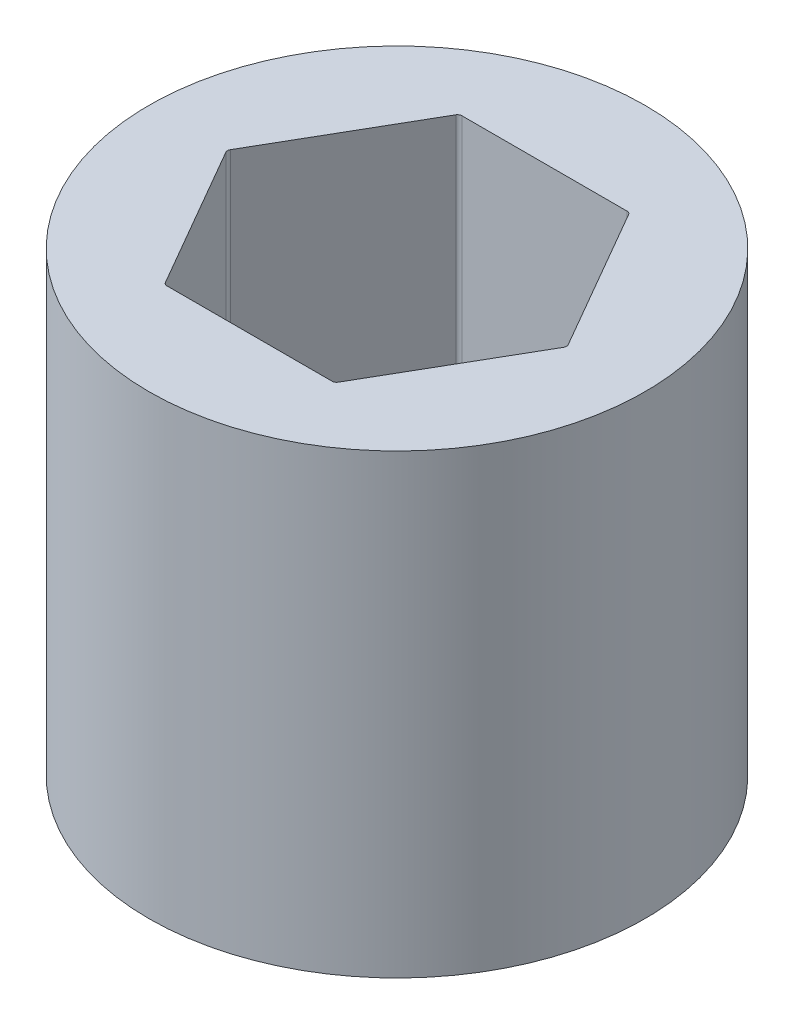
SolidWorks part; units mm, degrees
material "Nylon 101"
ref_plane "Front Plane" through (0, 0, 0) normal (0, 0, 1) x (1, 0, 0)
ref_plane "Top Plane" through (0, 0, 0) normal (0, 1, 0) x (1, 0, 0)
ref_plane "Right Plane" through (0, 0, 0) normal (1, 0, 0) x (0, 0, -1)
sketch "Sketch1" plane through (0, 0, 0) normal (0, 1, 0) x (1, 0, 0)
  line L1 (7.6256, 0) -> (3.8128, 6.604)
  line L2 (3.8128, 6.604) -> (-3.8128, 6.604)
  line L3 (-3.8128, 6.604) -> (-7.6256, 0)
  line L4 (-7.6256, 0) -> (-3.8128, -6.604)
  line L5 (-3.8128, -6.604) -> (3.8128, -6.604)
  line L6 (3.8128, -6.604) -> (7.6256, 0)
  circle A0 centre (0, 0) radius 11.1125
  circle A1 centre (0, 0) radius 6.604 construction
  dimension "D1" = 13.208
  dimension "D2" = 22.225
extrude "Boss-Extrude1" add sketch "Sketch1" along normal blind 20.447
fillet "Fillet1" radius 0.2 6 edges at (3.8128, 10.2235, -6.604) (-3.8128, 10.2235, -6.604) (-7.6256, 10.2235, 0) (3.8128, 10.2235, 6.604) (7.6256, 10.2235, 0) (-3.8128, 10.2235, 6.604)
